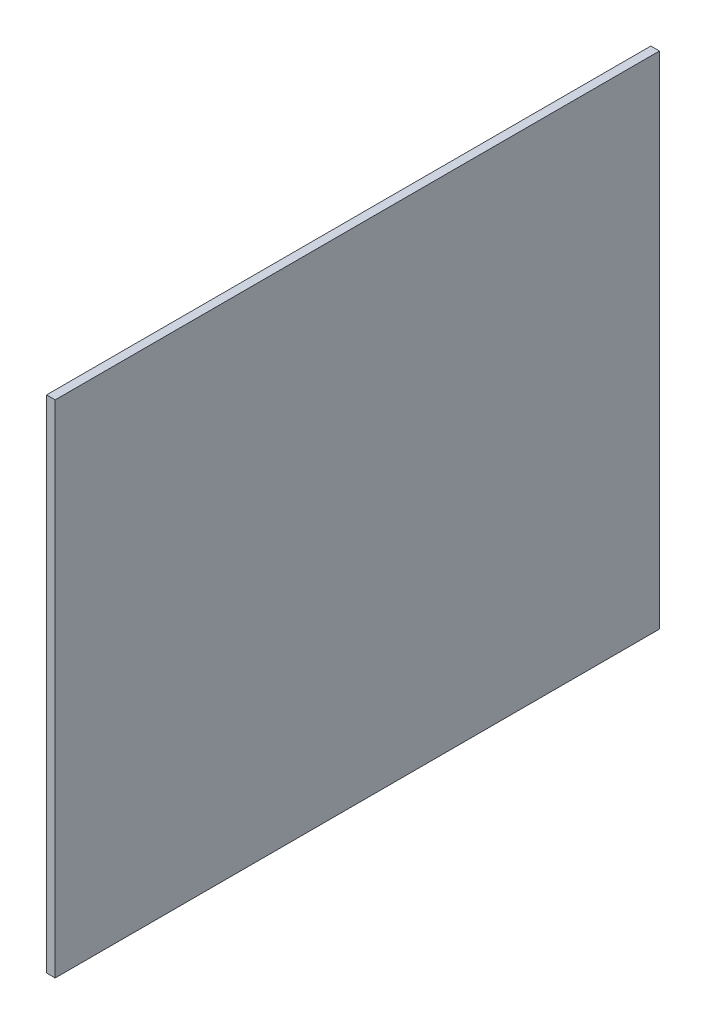
SolidWorks part; units mm, degrees
ref_plane "前视基准面" through (0, 0, 0) normal (0, 0, 1) x (1, 0, 0)
ref_plane "上视基准面" through (0, 0, 0) normal (0, 1, 0) x (1, 0, 0)
ref_plane "右视基准面" through (0, 0, 0) normal (1, 0, 0) x (0, 0, -1)
other "Configuration Table"
sketch "草图1" plane through (0, 0, 0) normal (1, 0, 0) x (0, 0, -1)
  line L1 (0, 0) -> (700, 0)
  line L2 (0, 0) -> (0, 580)
  line L3 (0, 580) -> (700, 580)
  line L4 (700, 0) -> (700, 580)
  dimension "D1" = 700
  dimension "D2" = 580
extrude "凸台-拉伸1" add sketch "草图1" along normal blind 10
